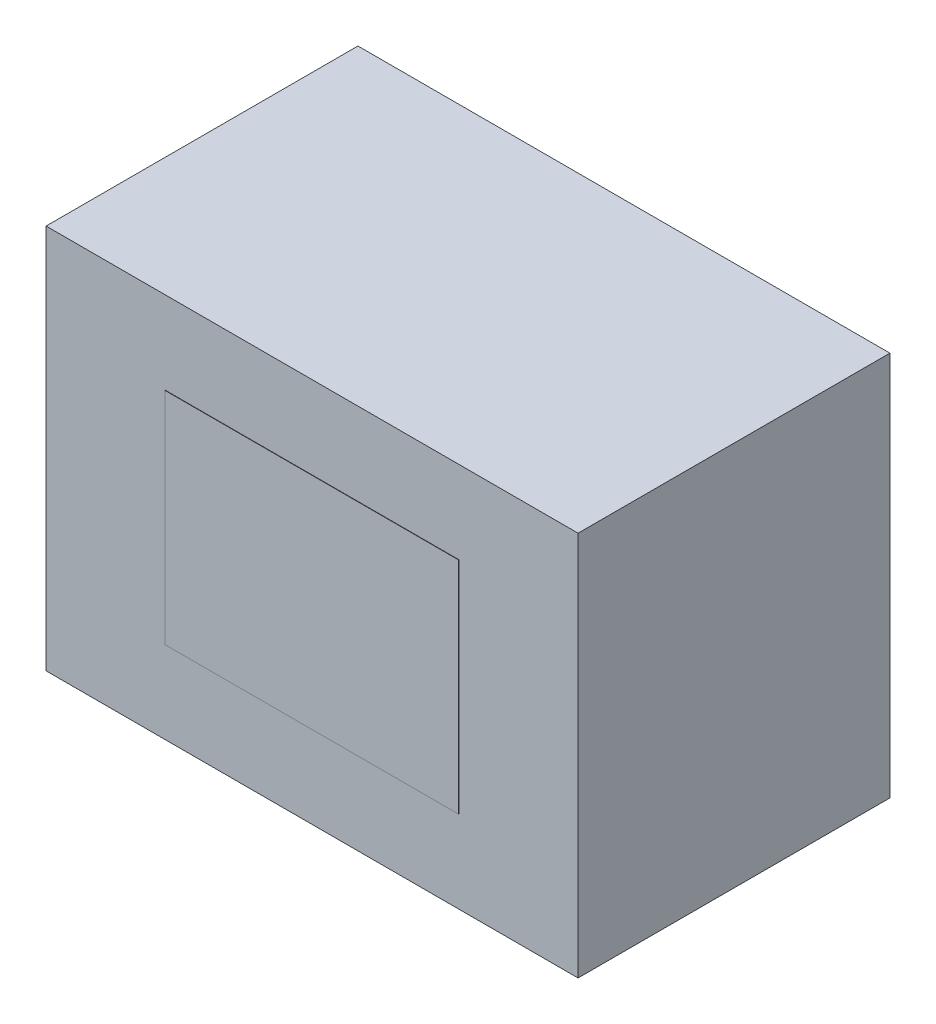
SolidWorks part; units mm, degrees
ref_plane "Front" through (0, 0, 0) normal (0, 0, 1) x (1, 0, 0)
ref_plane "Top" through (0, 0, 0) normal (0, 1, 0) x (1, 0, 0)
ref_plane "Right" through (0, 0, 0) normal (1, 0, 0) x (0, 0, -1)
sketch "Sketch1" plane through (0, 0, 0) normal (0, 0, 1) x (1, 0, 0)
  line L1 (88.9, -63.5) -> (-88.9, -63.5)
  line L2 (88.9, -63.5) -> (88.9, 63.5)
  line L3 (88.9, 63.5) -> (-88.9, 63.5)
  line L4 (-88.9, -63.5) -> (-88.9, 63.5)
  line L5 (88.9, -63.5) -> (-88.9, 63.5) construction
  line L6 (88.9, 63.5) -> (-88.9, -63.5) construction
  point P0 (0, 0)
  dimension "D1" = 177.8
  dimension "D2" = 127
extrude "Boss-Extrude1" add sketch "Sketch1" along normal blind 101.6
other "Move Face1" face at (0, -63.5, 50.8) face at (0, 0, 0) face at (-88.9, 0, 50.8) face at (88.9, 0, 50.8) face at (0, 63.5, 50.8) face at (0, 0, 101.6) parameters "D1"=3.175
sketch "Sketch2" plane through (0, 0, 104.775) normal (0, 0, 1) x (1, 0, 0)
  line L1 (-50.8, -38.1) -> (50.8, -38.1)
  line L2 (-50.8, -38.1) -> (-50.8, 38.1)
  line L3 (-50.8, 38.1) -> (50.8, 38.1)
  line L4 (50.8, -38.1) -> (50.8, 38.1)
  line L5 (-50.8, -38.1) -> (50.8, 38.1) construction
  line L6 (-50.8, 38.1) -> (50.8, -38.1) construction
  point P0 (0, 0)
  dimension "D1" = 76.2
  dimension "D2" = 101.6
extrude "Boss-Extrude2" add sketch "Sketch2" along normal blind 0.127
